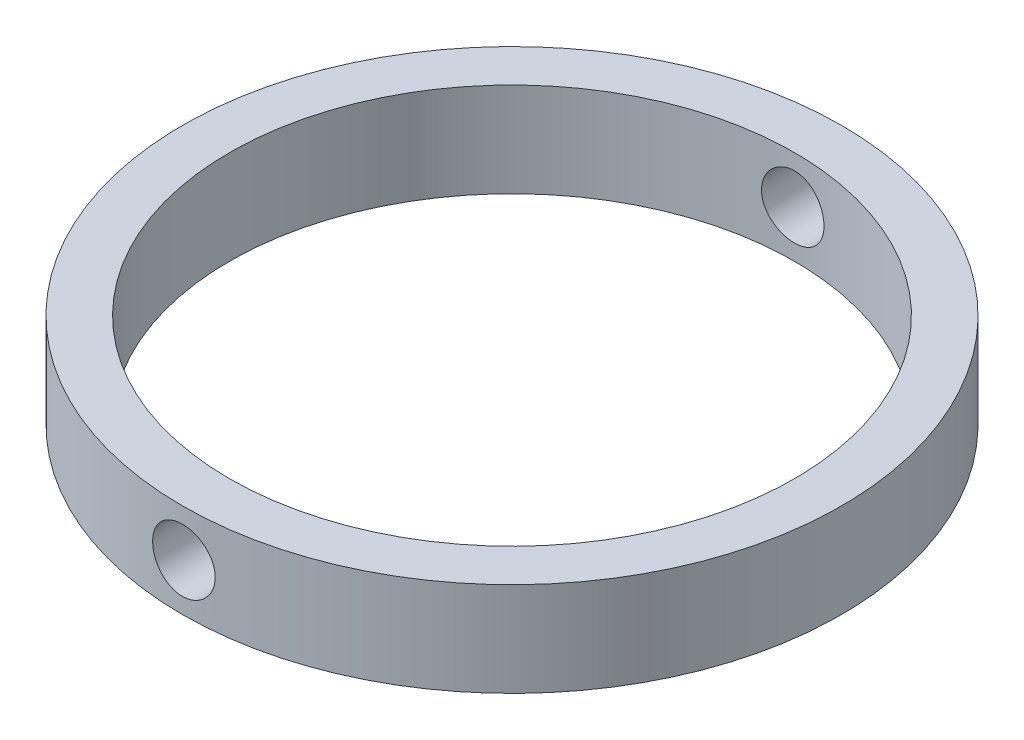
SolidWorks part; units mm, degrees
material "C (Graphite)"
ref_plane "Front Plane" through (0, 0, 0) normal (0, 0, 1) x (1, 0, 0)
ref_plane "Top Plane" through (0, 0, 0) normal (0, 1, 0) x (1, 0, 0)
ref_plane "Right Plane" through (0, 0, 0) normal (1, 0, 0) x (0, 0, -1)
sketch "Sketch1" plane through (0, 0, 0) normal (0, 1, 0) x (1, 0, 0)
  circle A0 centre (0, 0) radius 44.45
  circle A1 centre (0, 0) radius 38.1
  dimension "D1" = 88.9
  dimension "D2" = 76.2
extrude "Boss-Extrude1" add sketch "Sketch1" along normal blind 12.7
sketch "Sketch2" plane through (0, 0, 0) normal (0, 0, 1) x (1, 0, 0)
  line L0 (0, 0) -> (0, 12.7) construction
  line L1 (38.1, 12.7) -> (-38.1, 12.7) construction
  circle A0 centre (0, 6.35) radius 4.2164
  dimension "D1" = 8.4328
extrude "Cut-Extrude1" cut sketch "Sketch2" against normal through all both and the other way through all
